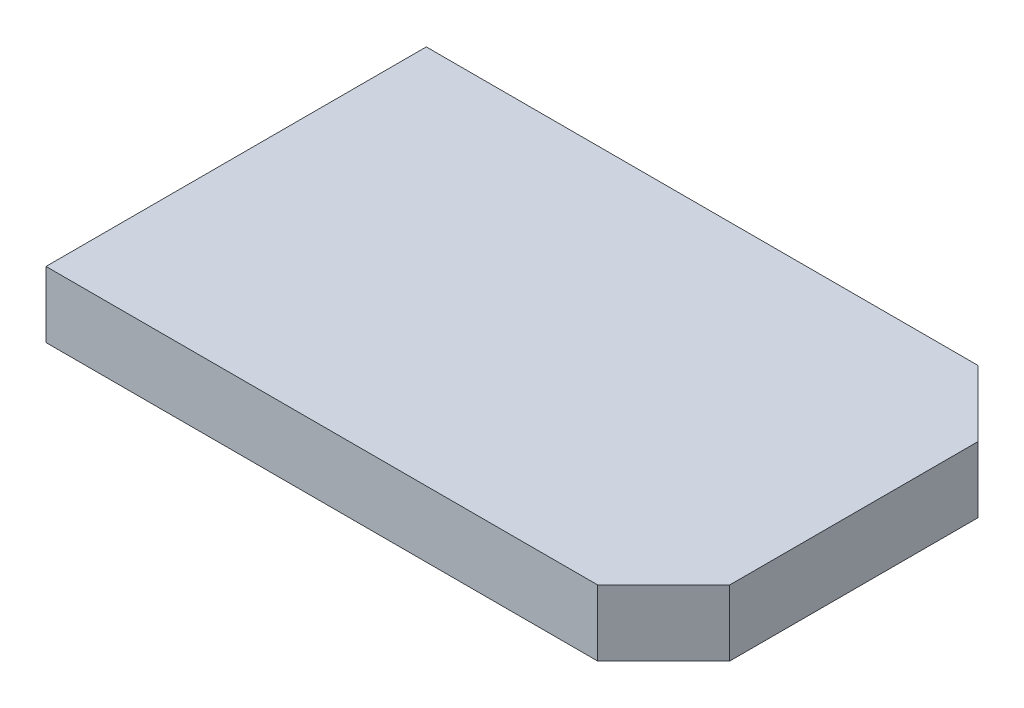
SolidWorks part; units mm, degrees
ref_plane "Front Plane" through (0, 0, 0) normal (0, 0, 1) x (1, 0, 0)
ref_plane "Top Plane" through (0, 0, 0) normal (0, 1, 0) x (1, 0, 0)
ref_plane "Right Plane" through (0, 0, 0) normal (1, 0, 0) x (0, 0, -1)
sketch "Sketch1" plane through (0, 0, 0) normal (0, 1, 0) x (1, 0, 0)
  line L1 (-56.1921, 34.5944) -> (56.1921, 34.5944)
  line L2 (-56.1921, 34.5944) -> (-56.1921, -34.5944)
  line L3 (-56.1921, -34.5944) -> (56.1921, -34.5944)
  line L4 (56.1921, 34.5944) -> (56.1921, -34.5944)
  line L5 (-56.1921, 34.5944) -> (56.1921, -34.5944) construction
  line L6 (-56.1921, -34.5944) -> (56.1921, 34.5944) construction
  point P0 (0, 0)
  point P6 (0, 0)
extrude "Boss-Extrude1" add sketch "Sketch1" along normal blind 12
chamfer "Chamfer3" distance 12 angle 45 1 edges at (56.1921, 6, 34.5944)
chamfer "Chamfer4" distance 12 angle 45 1 edges at (56.1921, 6, -34.5944)
